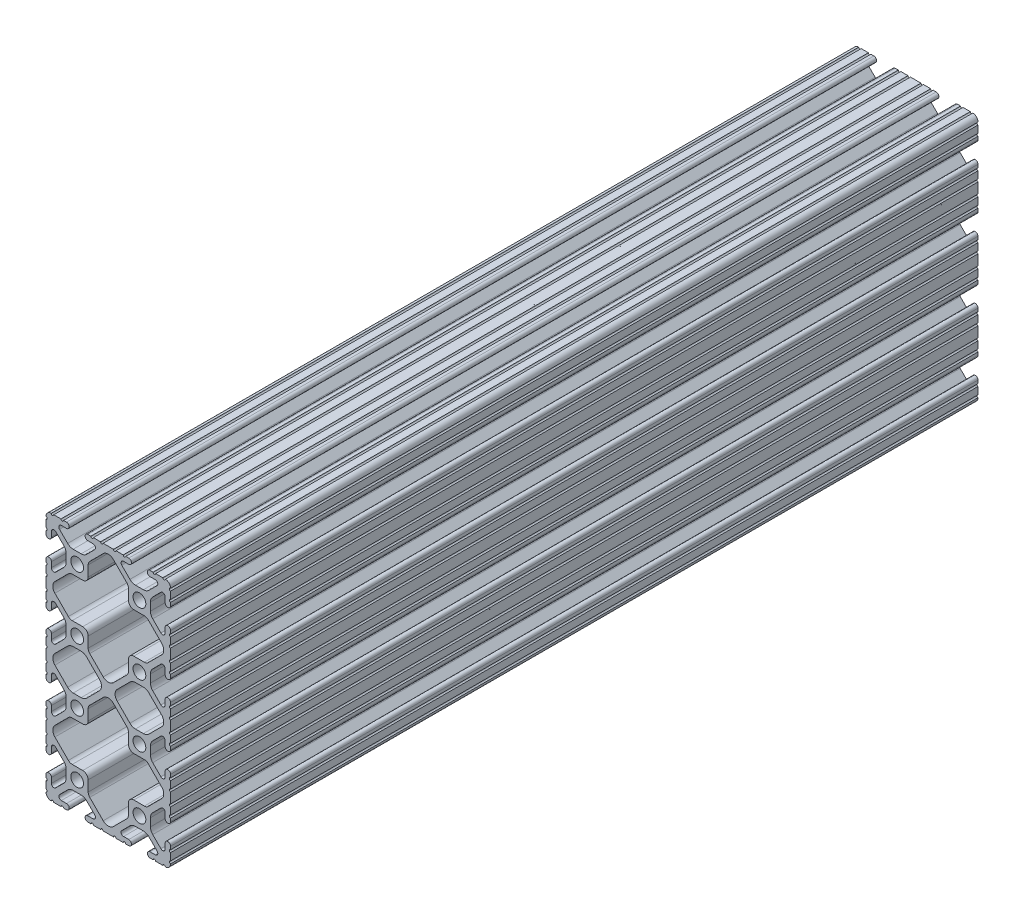
SolidWorks part; units mm, degrees
ref_plane "Front Plane" through (0, 0, 0) normal (0, 0, 1) x (1, 0, 0)
ref_plane "Top Plane" through (0, 0, 0) normal (0, 1, 0) x (1, 0, 0)
ref_plane "Right Plane" through (0, 0, 0) normal (1, 0, 0) x (0, 0, -1)
sketch "Sketch1" plane through (0, 0, 0) normal (0, 0, 1) x (1, 0, 0)
  line L0 (2.286, 55.2958) -> (-2.0184, 55.2958)
  line L1 (-3.5809, 55.943) -> (-9.0725, 61.4345)
  line L2 (-9.0725, 65.5655) -> (-3.5809, 71.057)
  line L3 (-2.0184, 71.7042) -> (2.286, 71.7042)
  line L4 (4.4958, 73.914) -> (4.4958, 78.2184)
  line L5 (5.143, 79.7809) -> (10.6345, 85.2725)
  line L6 (14.7655, 85.2725) -> (20.257, 79.7809)
  line L7 (20.9042, 78.2184) -> (20.9042, 73.914)
  line L8 (23.114, 71.7042) -> (27.4184, 71.7042)
  line L9 (28.9809, 71.057) -> (34.4725, 65.5655)
  line L10 (34.4725, 61.4345) -> (28.9809, 55.943)
  line L11 (27.4184, 55.2958) -> (23.114, 55.2958)
  line L12 (20.9042, 53.086) -> (20.9042, 48.7816)
  line L13 (20.257, 47.2191) -> (14.7655, 41.7275)
  line L14 (10.6345, 41.7275) -> (5.143, 47.2191)
  line L15 (4.4958, 48.7816) -> (4.4958, 53.086)
  line L16 (4.4958, 23.114) -> (4.4958, 27.4184)
  line L17 (5.143, 28.9809) -> (10.6345, 34.4725)
  line L18 (14.7655, 34.4725) -> (20.257, 28.9809)
  line L19 (20.9042, 27.4184) -> (20.9042, 23.114)
  line L20 (23.114, 20.9042) -> (27.4184, 20.9042)
  line L21 (28.9809, 20.257) -> (34.4725, 14.7655)
  line L22 (34.4725, 10.6345) -> (28.9809, 5.143)
  line L23 (27.4184, 4.4958) -> (23.114, 4.4958)
  line L24 (20.9042, 2.286) -> (20.9042, -2.0184)
  line L25 (20.257, -3.5809) -> (14.7655, -9.0725)
  line L26 (10.6345, -9.0725) -> (5.143, -3.5809)
  line L27 (4.4958, -2.0184) -> (4.4958, 2.286)
  line L28 (2.286, 4.4958) -> (-2.0184, 4.4958)
  line L29 (-3.5809, 5.143) -> (-9.0725, 10.6345)
  line L30 (-9.0725, 14.7655) -> (-3.5809, 20.257)
  line L31 (-2.0184, 20.9042) -> (2.286, 20.9042)
  line L32 (27.0186, 29.8958) -> (23.7824, 29.8958)
  line L33 (21.5373, 30.8258) -> (16.3286, 36.0346)
  line L34 (16.3286, 40.1654) -> (21.5373, 45.3742)
  line L35 (23.7824, 46.3042) -> (27.0186, 46.3042)
  line L36 (29.2636, 45.3743) -> (34.4725, 40.1655)
  line L37 (34.4725, 36.0345) -> (29.2636, 30.8257)
  line L38 (1.6176, 29.8958) -> (-1.6186, 29.8958)
  line L39 (-3.8636, 30.8257) -> (-9.0725, 36.0345)
  line L40 (-9.0725, 40.1655) -> (-3.8636, 45.3743)
  line L41 (-1.6186, 46.3042) -> (1.6176, 46.3042)
  line L42 (3.8627, 45.3742) -> (9.0714, 40.1654)
  line L43 (9.0714, 36.0346) -> (3.8627, 30.8258)
  line L44 (-12.7, 40.2336) -> (-12.7, 35.9664)
  line L45 (-12.7, 34.9504) -> (-12.7, 32.004)
  line L46 (-12.7, 30.988) -> (-12.7, 29.7434)
  line L47 (-10.4902, 29.7434) -> (-10.4902, 31.8743)
  line L48 (-8.7558, 32.5927) -> (-5.4258, 29.2627)
  line L49 (-4.4958, 27.0176) -> (-4.4958, 23.7824)
  line L50 (-5.4258, 21.5373) -> (-8.7558, 18.2073)
  line L51 (-10.4902, 18.9257) -> (-10.4902, 21.0566)
  line L52 (-12.7, 21.0566) -> (-12.7, 19.812)
  line L53 (-12.7, 18.796) -> (-12.7, 15.8496)
  line L54 (-12.7, 14.8336) -> (-12.7, 10.5664)
  line L55 (-12.7, 9.5504) -> (-12.7, 6.604)
  line L56 (-12.7, 5.588) -> (-12.7, 4.3434)
  line L57 (-10.4902, 4.3434) -> (-10.4902, 6.4743)
  line L58 (-8.7558, 7.1927) -> (-5.4258, 3.8627)
  line L59 (-4.4958, 1.6176) -> (-4.4958, -1.6176)
  line L60 (-5.4258, -3.8627) -> (-8.7558, -7.1927)
  line L61 (-10.4902, -6.4743) -> (-10.4902, -4.3434)
  line L62 (-12.7, -4.3434) -> (-12.7, -5.588)
  line L63 (-12.7, -6.604) -> (-12.7, -9.5504)
  line L64 (-9.5504, -12.7) -> (-6.604, -12.7)
  line L65 (-5.588, -12.7) -> (-4.3434, -12.7)
  line L66 (-4.3434, -10.4902) -> (-6.4743, -10.4902)
  line L67 (-7.1927, -8.7558) -> (-3.8627, -5.4258)
  line L68 (-1.6176, -4.4958) -> (1.6176, -4.4958)
  line L69 (3.8627, -5.4258) -> (7.1927, -8.7558)
  line L70 (6.4743, -10.4902) -> (4.3434, -10.4902)
  line L71 (4.3434, -12.7) -> (5.588, -12.7)
  line L72 (6.604, -12.7) -> (9.5504, -12.7)
  line L73 (10.5664, -12.7) -> (14.8336, -12.7)
  line L74 (15.8496, -12.7) -> (18.796, -12.7)
  line L75 (19.812, -12.7) -> (21.0566, -12.7)
  line L76 (21.0566, -10.4902) -> (18.9257, -10.4902)
  line L77 (18.2073, -8.7558) -> (21.5373, -5.4258)
  line L78 (23.7824, -4.4958) -> (27.0176, -4.4958)
  line L79 (29.2627, -5.4258) -> (32.5927, -8.7558)
  line L80 (31.8743, -10.4902) -> (29.7434, -10.4902)
  line L81 (29.7434, -12.7) -> (30.988, -12.7)
  line L82 (32.004, -12.7) -> (34.9504, -12.7)
  line L83 (38.1, -9.5504) -> (38.1, -6.604)
  line L84 (38.1, -5.588) -> (38.1, -4.3434)
  line L85 (35.8902, -4.3434) -> (35.8902, -6.4743)
  line L86 (34.1558, -7.1927) -> (30.8258, -3.8627)
  line L87 (29.8958, -1.6176) -> (29.8958, 1.6176)
  line L88 (30.8258, 3.8627) -> (34.1558, 7.1927)
  line L89 (35.8902, 6.4743) -> (35.8902, 4.3434)
  line L90 (38.1, 4.3434) -> (38.1, 5.588)
  line L91 (38.1, 6.604) -> (38.1, 9.5504)
  line L92 (38.1, 10.5664) -> (38.1, 14.8336)
  line L93 (38.1, 15.8496) -> (38.1, 18.796)
  line L94 (38.1, 19.812) -> (38.1, 21.0566)
  line L95 (35.8902, 21.0566) -> (35.8902, 18.9257)
  line L96 (34.1558, 18.2073) -> (30.8258, 21.5373)
  line L97 (29.8958, 23.7824) -> (29.8958, 27.0176)
  line L98 (30.8258, 29.2627) -> (34.1558, 32.5927)
  line L99 (35.8902, 31.8743) -> (35.8902, 29.7434)
  line L100 (38.1, 29.7434) -> (38.1, 30.988)
  line L101 (38.1, 32.004) -> (38.1, 34.9504)
  line L102 (38.1, 35.9664) -> (38.1, 40.2336)
  line L103 (38.1, 41.2496) -> (38.1, 44.196)
  line L104 (38.1, 45.212) -> (38.1, 46.4566)
  line L105 (35.8902, 46.4566) -> (35.8902, 44.3257)
  line L106 (34.1558, 43.6073) -> (30.8258, 46.9373)
  line L107 (29.8958, 49.1824) -> (29.8958, 52.4176)
  line L108 (30.8258, 54.6627) -> (34.1558, 57.9927)
  line L109 (35.8902, 57.2743) -> (35.8902, 55.1434)
  line L110 (38.1, 55.1434) -> (38.1, 56.388)
  line L111 (38.1, 57.404) -> (38.1, 60.3504)
  line L112 (38.1, 61.3664) -> (38.1, 65.6336)
  line L113 (38.1, 66.6496) -> (38.1, 69.596)
  line L114 (38.1, 70.612) -> (38.1, 71.8566)
  line L115 (35.8902, 71.8566) -> (35.8902, 69.7257)
  line L116 (34.1558, 69.0073) -> (30.8258, 72.3373)
  line L117 (29.8958, 74.5824) -> (29.8958, 77.8176)
  line L118 (30.8258, 80.0627) -> (34.1558, 83.3927)
  line L119 (35.8902, 82.6743) -> (35.8902, 80.5434)
  line L120 (38.1, 80.5434) -> (38.1, 81.788)
  line L121 (38.1, 82.804) -> (38.1, 85.7504)
  line L122 (34.9504, 88.9) -> (32.004, 88.9)
  line L123 (30.988, 88.9) -> (29.7434, 88.9)
  line L124 (29.7434, 86.6902) -> (31.8743, 86.6902)
  line L125 (32.5927, 84.9558) -> (29.2627, 81.6258)
  line L126 (27.0176, 80.6958) -> (23.7824, 80.6958)
  line L127 (21.5373, 81.6258) -> (18.2073, 84.9558)
  line L128 (18.9257, 86.6902) -> (21.0566, 86.6902)
  line L129 (21.0566, 88.9) -> (19.812, 88.9)
  line L130 (18.796, 88.9) -> (15.8496, 88.9)
  line L131 (14.8336, 88.9) -> (10.5664, 88.9)
  line L132 (9.5504, 88.9) -> (6.604, 88.9)
  line L133 (5.588, 88.9) -> (4.3434, 88.9)
  line L134 (4.3434, 86.6902) -> (6.4743, 86.6902)
  line L135 (7.1927, 84.9558) -> (3.8627, 81.6258)
  line L136 (1.6176, 80.6958) -> (-1.6176, 80.6958)
  line L137 (-3.8627, 81.6258) -> (-7.1927, 84.9558)
  line L138 (-6.4743, 86.6902) -> (-4.3434, 86.6902)
  line L139 (-4.3434, 88.9) -> (-5.588, 88.9)
  line L140 (-6.604, 88.9) -> (-9.5504, 88.9)
  line L141 (-12.7, 85.7504) -> (-12.7, 82.804)
  line L142 (-12.7, 81.788) -> (-12.7, 80.5434)
  line L143 (-10.4902, 80.5434) -> (-10.4902, 82.6743)
  line L144 (-8.7558, 83.3927) -> (-5.4258, 80.0627)
  line L145 (-4.4958, 77.8176) -> (-4.4958, 74.5824)
  line L146 (-5.4258, 72.3373) -> (-8.7558, 69.0073)
  line L147 (-10.4902, 69.7257) -> (-10.4902, 71.8566)
  line L148 (-12.7, 71.8566) -> (-12.7, 70.612)
  line L149 (-12.7, 69.596) -> (-12.7, 66.6496)
  line L150 (-12.7, 65.6336) -> (-12.7, 61.3664)
  line L151 (-12.7, 60.3504) -> (-12.7, 57.404)
  line L152 (-12.7, 56.388) -> (-12.7, 55.1434)
  line L153 (-10.4902, 55.1434) -> (-10.4902, 57.2743)
  line L154 (-8.7558, 57.9927) -> (-5.4258, 54.6627)
  line L155 (-4.4958, 52.4176) -> (-4.4958, 49.1824)
  line L156 (-5.4258, 46.9373) -> (-8.7558, 43.6073)
  line L157 (-10.4902, 44.3257) -> (-10.4902, 46.4566)
  line L158 (-12.7, 46.4566) -> (-12.7, 45.212)
  line L159 (-12.7, 44.196) -> (-12.7, 41.2496)
  arc A0 (4.4958, 53.086) -> (2.286, 55.2958) centre (2.286, 53.086) ccw
  arc A1 (-3.5809, 55.943) -> (-2.0184, 55.2958) centre (-2.0184, 57.5056) ccw
  arc A2 (-9.0725, 65.5655) -> (-9.0725, 61.4345) centre (-7.0071, 63.5) ccw
  arc A3 (-2.0184, 71.7042) -> (-3.5809, 71.057) centre (-2.0184, 69.4944) ccw
  arc A4 (2.286, 71.7042) -> (4.4958, 73.914) centre (2.286, 73.914) ccw
  arc A5 (5.143, 79.7809) -> (4.4958, 78.2184) centre (6.7056, 78.2184) ccw
  arc A6 (14.7655, 85.2725) -> (10.6345, 85.2725) centre (12.7, 83.2071) ccw
  arc A7 (20.9042, 78.2184) -> (20.257, 79.7809) centre (18.6944, 78.2184) ccw
  arc A8 (20.9042, 73.914) -> (23.114, 71.7042) centre (23.114, 73.914) ccw
  arc A9 (28.9809, 71.057) -> (27.4184, 71.7042) centre (27.4184, 69.4944) ccw
  arc A10 (34.4725, 61.4345) -> (34.4725, 65.5655) centre (32.4071, 63.5) ccw
  arc A11 (27.4184, 55.2958) -> (28.9809, 55.943) centre (27.4184, 57.5056) ccw
  arc A12 (23.114, 55.2958) -> (20.9042, 53.086) centre (23.114, 53.086) ccw
  arc A13 (20.257, 47.2191) -> (20.9042, 48.7816) centre (18.6944, 48.7816) ccw
  arc A14 (10.6345, 41.7275) -> (14.7655, 41.7275) centre (12.7, 43.7929) ccw
  arc A15 (4.4958, 48.7816) -> (5.143, 47.2191) centre (6.7056, 48.7816) ccw
  arc A16 (2.286, 20.9042) -> (4.4958, 23.114) centre (2.286, 23.114) ccw
  arc A17 (5.143, 28.9809) -> (4.4958, 27.4184) centre (6.7056, 27.4184) ccw
  arc A18 (14.7655, 34.4725) -> (10.6345, 34.4725) centre (12.7, 32.4071) ccw
  arc A19 (20.9042, 27.4184) -> (20.257, 28.9809) centre (18.6944, 27.4184) ccw
  arc A20 (20.9042, 23.114) -> (23.114, 20.9042) centre (23.114, 23.114) ccw
  arc A21 (28.9809, 20.257) -> (27.4184, 20.9042) centre (27.4184, 18.6944) ccw
  arc A22 (34.4725, 10.6345) -> (34.4725, 14.7655) centre (32.4071, 12.7) ccw
  arc A23 (27.4184, 4.4958) -> (28.9809, 5.143) centre (27.4184, 6.7056) ccw
  arc A24 (23.114, 4.4958) -> (20.9042, 2.286) centre (23.114, 2.286) ccw
  arc A25 (20.257, -3.5809) -> (20.9042, -2.0184) centre (18.6944, -2.0184) ccw
  arc A26 (10.6345, -9.0725) -> (14.7655, -9.0725) centre (12.7, -7.0071) ccw
  arc A27 (4.4958, -2.0184) -> (5.143, -3.5809) centre (6.7056, -2.0184) ccw
  arc A28 (4.4958, 2.286) -> (2.286, 4.4958) centre (2.286, 2.286) ccw
  arc A29 (-3.5809, 5.143) -> (-2.0184, 4.4958) centre (-2.0184, 6.7056) ccw
  arc A30 (-9.0725, 14.7655) -> (-9.0725, 10.6345) centre (-7.0071, 12.7) ccw
  arc A31 (-2.0184, 20.9042) -> (-3.5809, 20.257) centre (-2.0184, 18.6944) ccw
  arc A32 (27.0186, 29.8958) -> (29.2636, 30.8257) centre (27.0186, 33.0708) ccw
  arc A33 (21.5373, 30.8258) -> (23.7824, 29.8958) centre (23.7824, 33.0708) ccw
  arc A34 (16.3286, 40.1654) -> (16.3286, 36.0346) centre (18.3941, 38.1) ccw
  arc A35 (23.7824, 46.3042) -> (21.5373, 45.3742) centre (23.7824, 43.1292) ccw
  arc A36 (29.2636, 45.3743) -> (27.0186, 46.3042) centre (27.0186, 43.1292) ccw
  arc A37 (34.4725, 36.0345) -> (34.4725, 40.1655) centre (32.4071, 38.1) ccw
  arc A38 (1.6176, 29.8958) -> (3.8627, 30.8258) centre (1.6176, 33.0708) ccw
  arc A39 (-3.8636, 30.8257) -> (-1.6186, 29.8958) centre (-1.6186, 33.0708) ccw
  arc A40 (-9.0725, 40.1655) -> (-9.0725, 36.0345) centre (-7.0071, 38.1) ccw
  arc A41 (-1.6186, 46.3042) -> (-3.8636, 45.3743) centre (-1.6186, 43.1292) ccw
  arc A42 (3.8627, 45.3742) -> (1.6176, 46.3042) centre (1.6176, 43.1292) ccw
  arc A43 (9.0714, 36.0346) -> (9.0714, 40.1654) centre (7.0059, 38.1) ccw
  circle A44 centre (25.4, 76.2) radius 2.6035
  circle A45 centre (0, 76.2) radius 2.6035
  circle A46 centre (25.4, 50.8) radius 2.6035
  circle A47 centre (0, 50.8) radius 2.6035
  circle A48 centre (25.4, 0) radius 2.6035
  circle A49 centre (0, 0) radius 2.6035
  circle A50 centre (25.4, 25.4) radius 2.6035
  circle A51 centre (0, 25.4) radius 2.6035
  arc A52 (-12.7, 34.9504) -> (-12.7, 35.9664) centre (-12.7, 35.4584) ccw
  arc A53 (-12.7, 30.988) -> (-12.7, 32.004) centre (-12.7, 31.496) ccw
  arc A54 (-12.7, 29.7434) -> (-10.4902, 29.7434) centre (-11.5951, 29.7434) ccw
  arc A55 (-8.7558, 32.5927) -> (-10.4902, 31.8743) centre (-9.4742, 31.8743) ccw
  arc A56 (-4.4958, 27.0176) -> (-5.4258, 29.2627) centre (-7.6708, 27.0176) ccw
  arc A57 (-5.4258, 21.5373) -> (-4.4958, 23.7824) centre (-7.6708, 23.7824) ccw
  arc A58 (-10.4902, 18.9257) -> (-8.7558, 18.2073) centre (-9.4742, 18.9257) ccw
  arc A59 (-10.4902, 21.0566) -> (-12.7, 21.0566) centre (-11.5951, 21.0566) ccw
  arc A60 (-12.7, 18.796) -> (-12.7, 19.812) centre (-12.7, 19.304) ccw
  arc A61 (-12.7, 14.8336) -> (-12.7, 15.8496) centre (-12.7, 15.3416) ccw
  arc A62 (-12.7, 9.5504) -> (-12.7, 10.5664) centre (-12.7, 10.0584) ccw
  arc A63 (-12.7, 5.588) -> (-12.7, 6.604) centre (-12.7, 6.096) ccw
  arc A64 (-12.7, 4.3434) -> (-10.4902, 4.3434) centre (-11.5951, 4.3434) ccw
  arc A65 (-8.7558, 7.1927) -> (-10.4902, 6.4743) centre (-9.4742, 6.4743) ccw
  arc A66 (-4.4958, 1.6176) -> (-5.4258, 3.8627) centre (-7.6708, 1.6176) ccw
  arc A67 (-5.4258, -3.8627) -> (-4.4958, -1.6176) centre (-7.6708, -1.6176) ccw
  arc A68 (-10.4902, -6.4743) -> (-8.7558, -7.1927) centre (-9.4742, -6.4743) ccw
  arc A69 (-10.4902, -4.3434) -> (-12.7, -4.3434) centre (-11.5951, -4.3434) ccw
  arc A70 (-12.7, -6.604) -> (-12.7, -5.588) centre (-12.7, -6.096) ccw
  arc A71 (-12.6998, -10.5664) -> (-12.7, -9.5504) centre (-12.7, -10.0584) ccw
  arc A72 (-12.6998, -10.5664) -> (-10.5664, -12.6998) centre (-10.5918, -10.5918) ccw
  arc A73 (-9.5504, -12.7) -> (-10.5664, -12.6998) centre (-10.0584, -12.7) ccw
  arc A74 (-5.588, -12.7) -> (-6.604, -12.7) centre (-6.096, -12.7) ccw
  arc A75 (-4.3434, -12.7) -> (-4.3434, -10.4902) centre (-4.3434, -11.5951) ccw
  arc A76 (-7.1927, -8.7558) -> (-6.4743, -10.4902) centre (-6.4743, -9.4742) ccw
  arc A77 (-1.6176, -4.4958) -> (-3.8627, -5.4258) centre (-1.6176, -7.6708) ccw
  arc A78 (3.8627, -5.4258) -> (1.6176, -4.4958) centre (1.6176, -7.6708) ccw
  arc A79 (6.4743, -10.4902) -> (7.1927, -8.7558) centre (6.4743, -9.4742) ccw
  arc A80 (4.3434, -10.4902) -> (4.3434, -12.7) centre (4.3434, -11.5951) ccw
  arc A81 (6.604, -12.7) -> (5.588, -12.7) centre (6.096, -12.7) ccw
  arc A82 (10.5664, -12.7) -> (9.5504, -12.7) centre (10.0584, -12.7) ccw
  arc A83 (15.8496, -12.7) -> (14.8336, -12.7) centre (15.3416, -12.7) ccw
  arc A84 (19.812, -12.7) -> (18.796, -12.7) centre (19.304, -12.7) ccw
  arc A85 (21.0566, -12.7) -> (21.0566, -10.4902) centre (21.0566, -11.5951) ccw
  arc A86 (18.2073, -8.7558) -> (18.9257, -10.4902) centre (18.9257, -9.4742) ccw
  arc A87 (23.7824, -4.4958) -> (21.5373, -5.4258) centre (23.7824, -7.6708) ccw
  arc A88 (29.2627, -5.4258) -> (27.0176, -4.4958) centre (27.0176, -7.6708) ccw
  arc A89 (31.8743, -10.4902) -> (32.5927, -8.7558) centre (31.8743, -9.4742) ccw
  arc A90 (29.7434, -10.4902) -> (29.7434, -12.7) centre (29.7434, -11.5951) ccw
  arc A91 (32.004, -12.7) -> (30.988, -12.7) centre (31.496, -12.7) ccw
  arc A92 (35.9664, -12.6998) -> (34.9504, -12.7) centre (35.4584, -12.7) ccw
  arc A93 (35.9664, -12.6998) -> (38.0998, -10.5664) centre (35.9918, -10.5918) ccw
  arc A94 (38.1, -9.5504) -> (38.0998, -10.5664) centre (38.1, -10.0584) ccw
  arc A95 (38.1, -5.588) -> (38.1, -6.604) centre (38.1, -6.096) ccw
  arc A96 (38.1, -4.3434) -> (35.8902, -4.3434) centre (36.9951, -4.3434) ccw
  arc A97 (34.1558, -7.1927) -> (35.8902, -6.4743) centre (34.8742, -6.4743) ccw
  arc A98 (29.8958, -1.6176) -> (30.8258, -3.8627) centre (33.0708, -1.6176) ccw
  arc A99 (30.8258, 3.8627) -> (29.8958, 1.6176) centre (33.0708, 1.6176) ccw
  arc A100 (35.8902, 6.4743) -> (34.1558, 7.1927) centre (34.8742, 6.4743) ccw
  arc A101 (35.8902, 4.3434) -> (38.1, 4.3434) centre (36.9951, 4.3434) ccw
  arc A102 (38.1, 6.604) -> (38.1, 5.588) centre (38.1, 6.096) ccw
  arc A103 (38.1, 10.5664) -> (38.1, 9.5504) centre (38.1, 10.0584) ccw
  arc A104 (38.1, 15.8496) -> (38.1, 14.8336) centre (38.1, 15.3416) ccw
  arc A105 (38.1, 19.812) -> (38.1, 18.796) centre (38.1, 19.304) ccw
  arc A106 (38.1, 21.0566) -> (35.8902, 21.0566) centre (36.9951, 21.0566) ccw
  arc A107 (34.1558, 18.2073) -> (35.8902, 18.9257) centre (34.8742, 18.9257) ccw
  arc A108 (29.8958, 23.7824) -> (30.8258, 21.5373) centre (33.0708, 23.7824) ccw
  arc A109 (30.8258, 29.2627) -> (29.8958, 27.0176) centre (33.0708, 27.0176) ccw
  arc A110 (35.8902, 31.8743) -> (34.1558, 32.5927) centre (34.8742, 31.8743) ccw
  arc A111 (35.8902, 29.7434) -> (38.1, 29.7434) centre (36.9951, 29.7434) ccw
  arc A112 (38.1, 32.004) -> (38.1, 30.988) centre (38.1, 31.496) ccw
  arc A113 (38.1, 35.9664) -> (38.1, 34.9504) centre (38.1, 35.4584) ccw
  arc A114 (38.1, 41.2496) -> (38.1, 40.2336) centre (38.1, 40.7416) ccw
  arc A115 (38.1, 45.212) -> (38.1, 44.196) centre (38.1, 44.704) ccw
  arc A116 (38.1, 46.4566) -> (35.8902, 46.4566) centre (36.9951, 46.4566) ccw
  arc A117 (34.1558, 43.6073) -> (35.8902, 44.3257) centre (34.8742, 44.3257) ccw
  arc A118 (29.8958, 49.1824) -> (30.8258, 46.9373) centre (33.0708, 49.1824) ccw
  arc A119 (30.8258, 54.6627) -> (29.8958, 52.4176) centre (33.0708, 52.4176) ccw
  arc A120 (35.8902, 57.2743) -> (34.1558, 57.9927) centre (34.8742, 57.2743) ccw
  arc A121 (35.8902, 55.1434) -> (38.1, 55.1434) centre (36.9951, 55.1434) ccw
  arc A122 (38.1, 57.404) -> (38.1, 56.388) centre (38.1, 56.896) ccw
  arc A123 (38.1, 61.3664) -> (38.1, 60.3504) centre (38.1, 60.8584) ccw
  arc A124 (38.1, 66.6496) -> (38.1, 65.6336) centre (38.1, 66.1416) ccw
  arc A125 (38.1, 70.612) -> (38.1, 69.596) centre (38.1, 70.104) ccw
  arc A126 (38.1, 71.8566) -> (35.8902, 71.8566) centre (36.9951, 71.8566) ccw
  arc A127 (34.1558, 69.0073) -> (35.8902, 69.7257) centre (34.8742, 69.7257) ccw
  arc A128 (29.8958, 74.5824) -> (30.8258, 72.3373) centre (33.0708, 74.5824) ccw
  arc A129 (30.8258, 80.0627) -> (29.8958, 77.8176) centre (33.0708, 77.8176) ccw
  arc A130 (35.8902, 82.6743) -> (34.1558, 83.3927) centre (34.8742, 82.6743) ccw
  arc A131 (35.8902, 80.5434) -> (38.1, 80.5434) centre (36.9951, 80.5434) ccw
  arc A132 (38.1, 82.804) -> (38.1, 81.788) centre (38.1, 82.296) ccw
  arc A133 (38.0998, 86.7664) -> (38.1, 85.7504) centre (38.1, 86.2584) ccw
  arc A134 (38.0998, 86.7664) -> (35.9664, 88.8998) centre (35.9918, 86.7918) ccw
  arc A135 (34.9504, 88.9) -> (35.9664, 88.8998) centre (35.4584, 88.9) ccw
  arc A136 (30.988, 88.9) -> (32.004, 88.9) centre (31.496, 88.9) ccw
  arc A137 (29.7434, 88.9) -> (29.7434, 86.6902) centre (29.7434, 87.7951) ccw
  arc A138 (32.5927, 84.9558) -> (31.8743, 86.6902) centre (31.8743, 85.6742) ccw
  arc A139 (27.0176, 80.6958) -> (29.2627, 81.6258) centre (27.0176, 83.8708) ccw
  arc A140 (21.5373, 81.6258) -> (23.7824, 80.6958) centre (23.7824, 83.8708) ccw
  arc A141 (18.9257, 86.6902) -> (18.2073, 84.9558) centre (18.9257, 85.6742) ccw
  arc A142 (21.0566, 86.6902) -> (21.0566, 88.9) centre (21.0566, 87.7951) ccw
  arc A143 (18.796, 88.9) -> (19.812, 88.9) centre (19.304, 88.9) ccw
  arc A144 (14.8336, 88.9) -> (15.8496, 88.9) centre (15.3416, 88.9) ccw
  arc A145 (9.5504, 88.9) -> (10.5664, 88.9) centre (10.0584, 88.9) ccw
  arc A146 (5.588, 88.9) -> (6.604, 88.9) centre (6.096, 88.9) ccw
  arc A147 (4.3434, 88.9) -> (4.3434, 86.6902) centre (4.3434, 87.7951) ccw
  arc A148 (7.1927, 84.9558) -> (6.4743, 86.6902) centre (6.4743, 85.6742) ccw
  arc A149 (1.6176, 80.6958) -> (3.8627, 81.6258) centre (1.6176, 83.8708) ccw
  arc A150 (-3.8627, 81.6258) -> (-1.6176, 80.6958) centre (-1.6176, 83.8708) ccw
  arc A151 (-6.4743, 86.6902) -> (-7.1927, 84.9558) centre (-6.4743, 85.6742) ccw
  arc A152 (-4.3434, 86.6902) -> (-4.3434, 88.9) centre (-4.3434, 87.7951) ccw
  arc A153 (-6.604, 88.9) -> (-5.588, 88.9) centre (-6.096, 88.9) ccw
  arc A154 (-10.5664, 88.8998) -> (-9.5504, 88.9) centre (-10.0584, 88.9) ccw
  arc A155 (-10.5664, 88.8998) -> (-12.6998, 86.7664) centre (-10.5918, 86.7918) ccw
  arc A156 (-12.7, 85.7504) -> (-12.6998, 86.7664) centre (-12.7, 86.2584) ccw
  arc A157 (-12.7, 81.788) -> (-12.7, 82.804) centre (-12.7, 82.296) ccw
  arc A158 (-12.7, 80.5434) -> (-10.4902, 80.5434) centre (-11.5951, 80.5434) ccw
  arc A159 (-8.7558, 83.3927) -> (-10.4902, 82.6743) centre (-9.4742, 82.6743) ccw
  arc A160 (-4.4958, 77.8176) -> (-5.4258, 80.0627) centre (-7.6708, 77.8176) ccw
  arc A161 (-5.4258, 72.3373) -> (-4.4958, 74.5824) centre (-7.6708, 74.5824) ccw
  arc A162 (-10.4902, 69.7257) -> (-8.7558, 69.0073) centre (-9.4742, 69.7257) ccw
  arc A163 (-10.4902, 71.8566) -> (-12.7, 71.8566) centre (-11.5951, 71.8566) ccw
  arc A164 (-12.7, 69.596) -> (-12.7, 70.612) centre (-12.7, 70.104) ccw
  arc A165 (-12.7, 65.6336) -> (-12.7, 66.6496) centre (-12.7, 66.1416) ccw
  arc A166 (-12.7, 60.3504) -> (-12.7, 61.3664) centre (-12.7, 60.8584) ccw
  arc A167 (-12.7, 56.388) -> (-12.7, 57.404) centre (-12.7, 56.896) ccw
  arc A168 (-12.7, 55.1434) -> (-10.4902, 55.1434) centre (-11.5951, 55.1434) ccw
  arc A169 (-8.7558, 57.9927) -> (-10.4902, 57.2743) centre (-9.4742, 57.2743) ccw
  arc A170 (-4.4958, 52.4176) -> (-5.4258, 54.6627) centre (-7.6708, 52.4176) ccw
  arc A171 (-5.4258, 46.9373) -> (-4.4958, 49.1824) centre (-7.6708, 49.1824) ccw
  arc A172 (-10.4902, 44.3257) -> (-8.7558, 43.6073) centre (-9.4742, 44.3257) ccw
  arc A173 (-10.4902, 46.4566) -> (-12.7, 46.4566) centre (-11.5951, 46.4566) ccw
  arc A174 (-12.7, 44.196) -> (-12.7, 45.212) centre (-12.7, 44.704) ccw
  arc A175 (-12.7, 40.2336) -> (-12.7, 41.2496) centre (-12.7, 40.7416) ccw
extrude "Extrude1" add sketch "Sketch1" against normal blind 329.311
